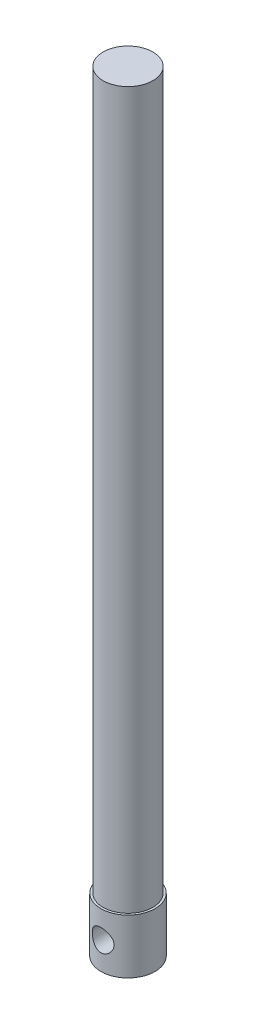
SolidWorks part; units mm, degrees
ref_plane "Alzado" through (0, 0, 0) normal (0, 0, 1) x (1, 0, 0)
ref_plane "Planta" through (0, 0, 0) normal (0, 1, 0) x (1, 0, 0)
ref_plane "Vista lateral" through (0, 0, 0) normal (1, 0, 0) x (0, 0, -1)
sketch "Sketch1" plane through (0, 0, 0) normal (0, 1, 0) x (1, 0, 0)
  circle A0 centre (0, 0) radius 3.937
  dimension "D1" = 7.874
extrude "Boss-Extrude1" add sketch "Sketch1" along normal blind 7.9248
sketch "Sketch3" plane through (0, 7.9248, 0) normal (0, 1, 0) x (1, 0, 0)
  circle A0 centre (0, 0) radius 3.6195
  dimension "D1" = 7.239
extrude "Boss-Extrude2" add sketch "Sketch3" along normal blind 104.14
sketch "Sketch4" plane through (0, 0, 0) normal (0, 0, 1) x (1, 0, 0)
  line L0 (0, 0) -> (0, 3.9624)
  circle A0 centre (0, 3.9624) radius 1.5875
  dimension "D2" = 3.175
  dimension "D1" = 3.9624
extrude "Cut-Extrude1" cut sketch "Sketch4" against normal through all both and the other way through all contours A0
sketch "Sketch5" plane through (0, 0, 0) normal (0, 0, 1) x (1, 0, 0)
  line L0 (0, 7.9248) -> (0, 15.875)
  line L1 (3.937, 7.9248) -> (-3.937, 7.9248) construction
  line L2 (0, 112.0648) -> (0, 101.0666)
  line L3 (3.6195, 112.0648) -> (-3.6195, 112.0648) construction
  point P9 (0, 0)
  dimension "D1" = 7.9502
  dimension "D2" = 10.9982
  dimension "D3" = 85.1916
ref_plane "Plane1" through (0, 15.875, 0) normal (0, 1, 0) x (1, 0, 0)
sketch "Sketch6" plane through (0, 15.875, 0) normal (0, 1, 0) x (1, 0, 0)
  circle A0 centre (0, 0) radius 3.6766
  dimension "D1" = 7.3533
curve "Helix/Spiral1" pitch 1.27 height 85.6996 turns 67.48
sketch "Sketch7" plane through (0, 0, 0) normal (1, 0, 0) x (0, 0, -1)
  line L1 (3.9814, 15.875) -> (-3.9814, 15.875) construction
  line L2 (3.6195, 7.9248) -> (3.6195, 112.0648) construction
  line L3 (3.6195, 15.367) -> (3.6195, 16.383)
  line L4 (3.6195, 16.383) -> (2.6162, 15.875)
  line L5 (3.6195, 15.367) -> (2.6162, 15.875)
